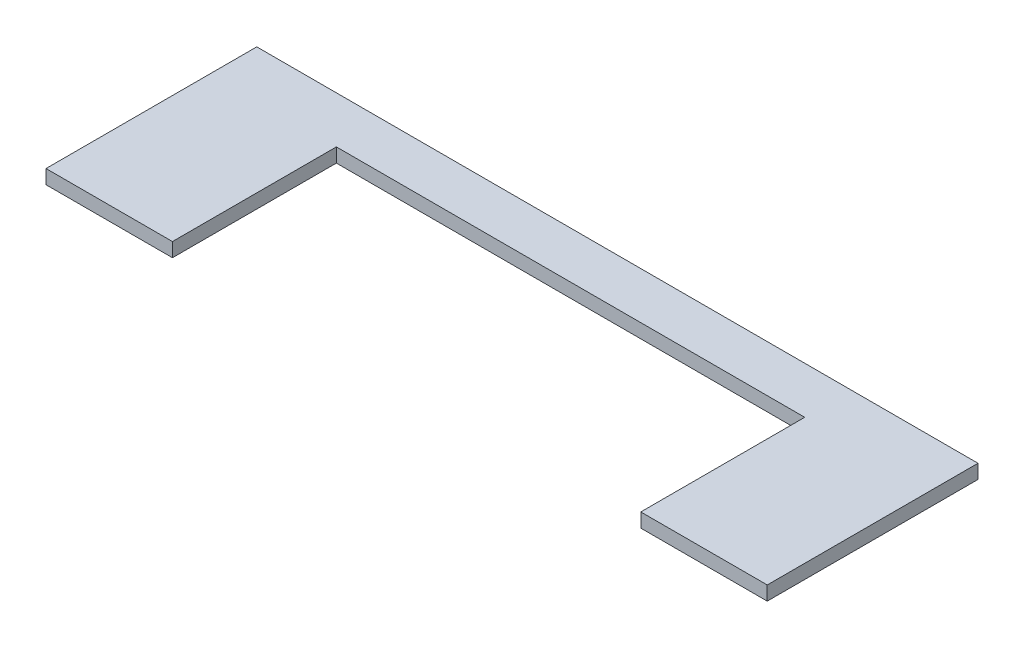
SolidWorks part; units mm, degrees
material "Plain Carbon Steel"
ref_plane "Front Plane" through (0, 0, 0) normal (0, 0, 1) x (1, 0, 0)
ref_plane "Top Plane" through (0, 0, 0) normal (0, 1, 0) x (1, 0, 0)
ref_plane "Right Plane" through (0, 0, 0) normal (1, 0, 0) x (0, 0, -1)
sketch "Sketch1" plane through (0, 0, 0) normal (0, 1, 0) x (1, 0, 0)
  line L0 (-39.3894, -45) -> (-39.3894, 25)
  line L1 (-93.3894, -45) -> (-39.3894, -45)
  line L2 (-93.3894, -45) -> (-93.3894, 45)
  line L3 (-93.3894, 45) -> (40.2283, 45)
  line L4 (214.6106, -45) -> (214.6106, 45)
  line L5 (160.6106, -45) -> (214.6106, -45)
  line L7 (-39.3894, 25) -> (160.6106, 25)
  line L8 (160.6106, 25) -> (160.6106, -45)
  line L9 (40.2283, 45) -> (214.6106, 45)
  point P0 (0, 0)
  dimension "D1" = 90
  dimension "D2" = 90
  dimension "D4" = 308
  dimension "D5" = 200
  dimension "D6" = 70
extrude "Boss-Extrude1" add sketch "Sketch1" along normal blind 6
